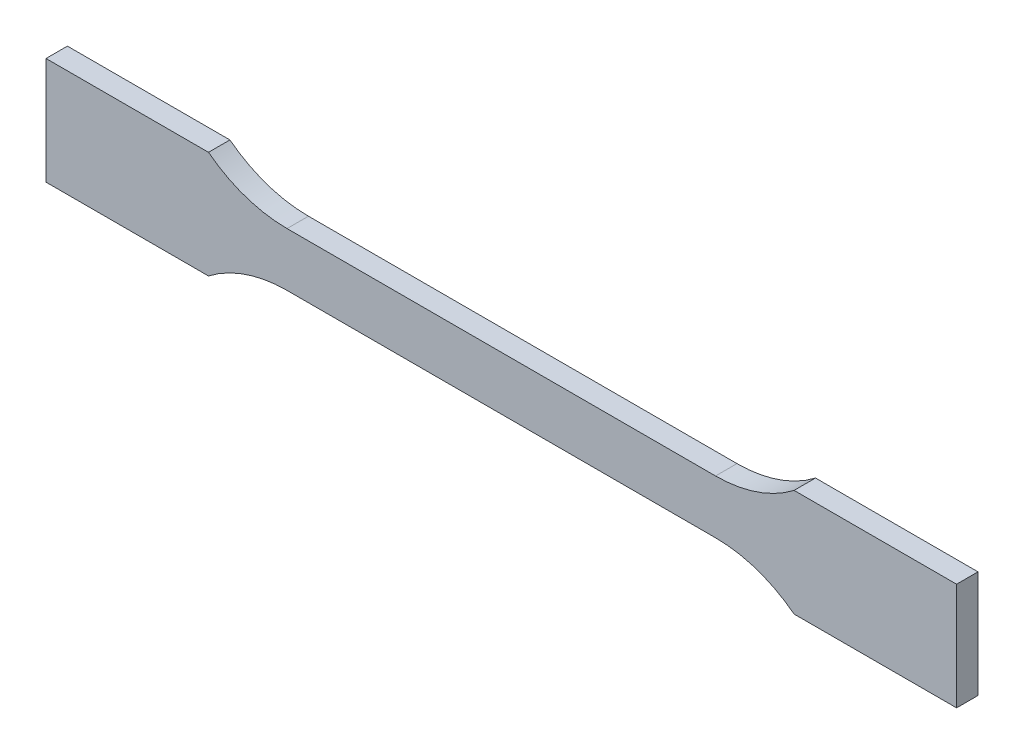
SolidWorks part; units mm, degrees
other "ISO_527-2_type_1A"
ref_plane "Front Plane" through (0, 0, 0) normal (0, 0, 1) x (1, 0, 0)
ref_plane "Top Plane" through (0, 0, 0) normal (0, 1, 0) x (1, 0, 0)
ref_plane "Right Plane" through (0, 0, 0) normal (1, 0, 0) x (0, 0, -1)
other "Configuration Table"
sketch "Sketch1" plane through (0, 0, 0) normal (0, 0, 1) x (1, 0, 0)
  line L0 (-85, 10) -> (-85, -10)
  line L1 (-85, -10) -> (-54.6629, -10)
  line L2 (-85, 10) -> (-54.6629, 10)
  line L3 (54.6629, 10) -> (85, 10)
  line L4 (85, 10) -> (85, -10)
  line L5 (85, -10) -> (54.6629, -10)
  line L6 (-40, 5) -> (40, 5)
  line L7 (-40, -5) -> (40, -5)
  arc A0 (-40, 5) -> (-54.6629, 10) centre (-40, 29) cw
  arc A1 (-40, -5) -> (-54.6629, -10) centre (-40, -29) ccw
  arc A2 (40, -5) -> (54.6629, -10) centre (40, -29) cw
  arc A3 (40, 5) -> (54.6629, 10) centre (40, 29) ccw
  point P8 (-85, 0)
  point P14 (0, 5)
  dimension "radius" = 24
  dimension "overall_length" = 170
  dimension "width_at_ends" = 20
  dimension "width_at_narrow_portion" = 10
  dimension "length_narrow_sided_portion" = 80
extrude "Boss-Extrude1" add sketch "Sketch1" along normal mid plane 4
